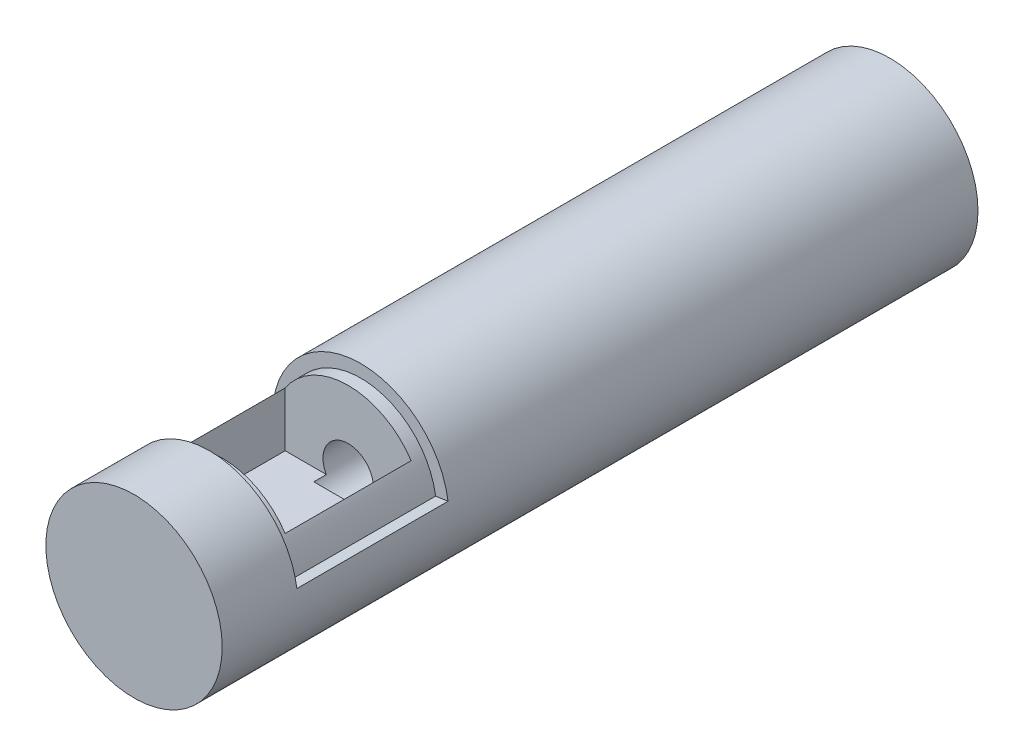
SolidWorks part; units mm, degrees
material "Teak"
ref_plane "Front Plane" through (0, 0, 0) normal (0, 0, 1) x (1, 0, 0)
ref_plane "Top Plane" through (0, 0, 0) normal (0, 1, 0) x (1, 0, 0)
ref_plane "Right Plane" through (0, 0, 0) normal (1, 0, 0) x (0, 0, -1)
sketch "Sketch2" plane through (0, 0, 0) normal (0, 0, 1) x (1, 0, 0)
  circle A0 centre (0, 0) radius 22.225
  dimension "D1" = 44.45
extrude "Boss-Extrude1" add sketch "Sketch2" against normal blind 190.5 contours A0
sketch "Sketch3" plane through (0, 0, -190.5) normal (0, 0, -1) x (-1, 0, 0)
  circle A0 centre (0, 0) radius 6.35
  dimension "D1" = 12.7
extrude "Cut-Extrude1" cut sketch "Sketch3" against normal blind 139.7
ref_plane "Plane1" through (0, 22.225, 0) normal (0, 1, 0) x (1, 0, 0)
sketch "Sketch4" plane through (0, 22.225, 0) normal (0, 1, 0) x (1, 0, 0)
  line L2 (-31.75, 19.05) -> (31.75, 19.05)
  line L3 (-31.75, 19.05) -> (-31.75, 57.15)
  line L4 (-31.75, 57.15) -> (31.75, 57.15)
  line L5 (31.75, 19.05) -> (31.75, 57.15)
  point P4 (0, 19.05)
  point P6 (0, 0)
  dimension "D1" = 19.05
  dimension "D2" = 38.1
  dimension "D3" = 63.5
wrap "Wrap1" sketch "Sketch4" wrap type deboss source sketch "Sketch4" thickness 3.175 face at (22.225, 0, -190.5) parameters "D1"=3.175
sketch "Sketch6" plane through (0, 22.225, 0) normal (0, 1, 0) x (1, 0, 0)
  line L0 (-18.8577, 57.15) -> (-18.8577, 19.05) construction
  line L1 (22.0006, 19.05) -> (-22.0006, 19.05) construction
  line L6 (-15.875, 22.225) -> (-15.875, 53.975)
  line L7 (-15.875, 53.975) -> (15.875, 53.975)
  line L8 (15.875, 22.225) -> (15.875, 53.975)
  line L9 (-15.875, 22.225) -> (15.875, 22.225)
  point P0 (0, 22.225)
  point P7 (0, 19.05)
  dimension "D1" = 31.75
  dimension "D2" = 31.75
extrude "Cut-Extrude2" cut sketch "Sketch6" against normal blind 25.4
sketch "Sketch7" plane through (0, 22.225, 0) normal (0, 1, 0) x (1, 0, 0)
  line L1 (-15.875, 22.225) -> (15.875, 22.225)
  line L2 (-15.875, 22.225) -> (-15.875, 53.975)
  line L3 (-15.875, 53.975) -> (15.875, 53.975)
  line L4 (15.875, 22.225) -> (15.875, 53.975)
  circle A0 centre (-8.255, 29.845) radius 1.1906
  circle A1 centre (8.255, 46.355) radius 1.1906
  dimension "D1" = 7.62
  dimension "D5" = 2.3813
  dimension "D6" = 2.3813
  dimension "D2" = 7.62
  dimension "D3" = 7.62
  dimension "D4" = 7.62
extrude "Cut-Extrude3" cut sketch "Sketch7" against normal offset from surface (31.75 mm away) 6.35 contours A0 | A1 up to face at (0, -3.175, -45.2437) offset beyond the face yes
ref_plane "Plane2" through (0, -22.225, 0) normal (0, -1, 0) x (-1, 0, 0)
sketch "Sketch8" plane through (0, -22.225, 0) normal (0, -1, 0) x (-1, 0, 0)
  line L0 (0, 190.5) -> (0, 97.882)
  line L1 (22.225, 190.5) -> (-22.225, 190.5) construction
  circle A0 centre (0, 174.625) radius 6.35
  dimension "D1" = 15.875
extrude "Cut-Extrude4" cut sketch "Sketch8" against normal blind 22.225 contours A0
